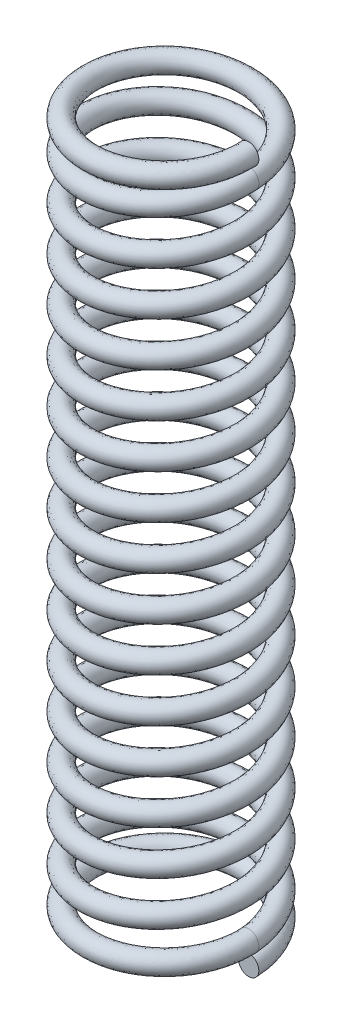
SolidWorks part; units mm, degrees
ref_plane "Front" through (0, 0, 0) normal (0, 0, 1) x (1, 0, 0)
ref_plane "Top" through (0, 0, 0) normal (0, 1, 0) x (1, 0, 0)
ref_plane "Right" through (0, 0, 0) normal (1, 0, 0) x (0, 0, -1)
sketch "Sketch1" plane through (0, 0, 0) normal (0, 0, 1) x (1, 0, 0)
  line L0 (2.8067, 25.4) -> (2.8067, 25.0317) construction
  line L1 (0, 0) -> (2.8067, 0) construction
  line L2 (0, 0) -> (0, 25.4) construction
  line L3 (0, 25.4) -> (2.8067, 25.4) construction
  line L4 (2.8067, 25.0317) -> (2.8067, 25.0063) construction
  line L5 (2.8067, 25.0063) -> (2.8067, 24.2697) construction
  line L6 (2.8067, 24.2697) -> (2.8067, 1.1303) construction
  line L7 (2.8067, 1.1303) -> (2.8067, 0.3937) construction
  line L8 (2.8067, 0.3937) -> (2.8067, 0.3683) construction
  line L9 (2.8067, 0.3683) -> (2.8067, 0) construction
  line L10 (2.8067, 0) -> (3.175, 0) construction
  line L11 (2.8067, 0.762) -> (3.175, 0.762) construction
  line L12 (2.8067, 25.4) -> (3.175, 25.4) construction
  line L13 (2.8067, 25.4) -> (2.8067, 25.7683) construction
  line L14 (2.8067, 0) -> (2.8067, -0.3683) construction
  circle A0 centre (2.8067, 25.4) radius 0.3683 construction
  circle A1 centre (2.8067, 24.638) radius 0.3683 construction
  circle A2 centre (2.8067, 0.762) radius 0.3683
  circle A3 centre (2.8067, 0) radius 0.3683 construction
  dimension "Wire Dia" = 0.7366
  dimension "D3" = 23.876
  dimension "D4" = 0.762
  dimension "D1" = 0.0254
  dimension "Spring-OD" = 6.35
  dimension "Overall Height" = 25.4
ref_plane "Plane1" through (0, 0.762, 0) normal (0, 1, 0) x (-1, 0, 0)
sketch "Sketch3" plane through (0, 0.762, 0) normal (0, 1, 0) x (-1, 0, 0)
  circle A0 centre (0, 0) radius 3.175
curve "Helix1" pitch 1.5917 height 23.876 turns 15
sweep "Sweep1" add profiles "Sketch1" path "Helix1"
sketch "Sketch4" plane through (0, 0.762, 0) normal (0, 1, 0) x (-1, 0, 0)
  circle A0 centre (0, 0) radius 3.175 construction
  circle A1 centre (0, 0) radius 3.175
curve "Helix2" pitch 0.762 height 0.762 turns 1
sketch "Sketch5" plane through (0, 0, 0) normal (0, 0, 1) x (1, 0, 0)
  circle A0 centre (2.8067, 0) radius 0.3683 construction
  circle A1 centre (2.8067, 0) radius 0.3683
sweep "Sweep2" add profiles "Sketch5" path "Helix2"
ref_plane "Plane2" through (0, 24.638, 0) normal (0, 1, 0) x (-1, 0, 0)
sketch "Sketch6" plane through (0, 24.638, 0) normal (0, 1, 0) x (-1, 0, 0)
  circle A0 centre (0, 0) radius 3.175 construction
  circle A1 centre (0, 0) radius 3.175
curve "Helix3" pitch 0.762 height 0.762 turns 1
sketch "Sketch7" plane through (0, 0, 0) normal (0, 0, 1) x (1, 0, 0)
  circle A0 centre (2.8067, 24.638) radius 0.3683 construction
  circle A1 centre (2.8067, 24.638) radius 0.3683
sweep "Sweep3" add profiles "Sketch7" path "Helix3"
equation "\"D3@Helix1\"=\"D3@Sketch1\""
equation "\"D3@Helix2\"=\"D4@Sketch1\""
equation "\"D3@Helix3\"=\"D4@Sketch1\""
